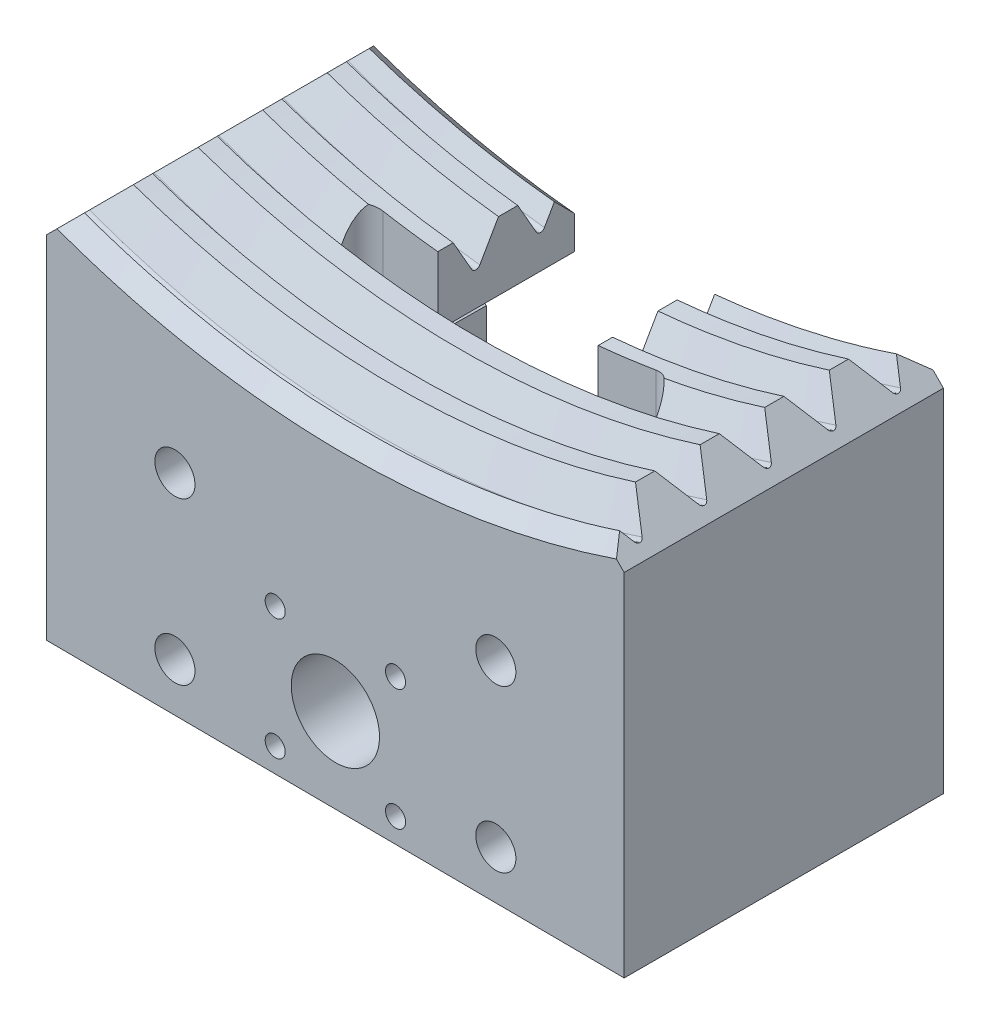
SolidWorks part; units mm, degrees
material "Nylon 101"
ref_plane "Ebene vorne" through (0, 0, 0) normal (0, 0, 1) x (1, 0, 0)
ref_plane "Ebene oben" through (0, 0, 0) normal (0, 1, 0) x (1, 0, 0)
ref_plane "Ebene rechts" through (0, 0, 0) normal (1, 0, 0) x (0, 0, -1)
sketch "Skizze1" plane through (0, 0, 0) normal (0, 0, 1) x (1, 0, 0)
  circle A0 centre (0, 0) radius 101
  circle A1 centre (0, 0) radius 225
  dimension "D1" = 202
  dimension "D2" = 450
extrude "Aufsatz-Linear austragen1" add sketch "Skizze1" along normal blind 40
chamfer "Fase1" distance 4.5 angle 45 2 edges at (101, 0, 40) (101, 0, 0)
sketch "Skizze32" plane through (0, 0, 40) normal (0, 0, 1) x (1, 0, 0)
  circle A0 centre (0, 0) radius 105
  dimension "D1" = 210
curve "Spirale/Helix1" pitch 8 height 50 turns 6.25
sketch "Skizze33" plane through (0, 0, 0) normal (1, 0, 0) x (0, 0, -1)
  line L0 (-40.5, 105.866) -> (-36.5, 98.9378) construction
  line L1 (-36.5, 98.9378) -> (-44.5, 98.9378) construction
  line L2 (-44.5, 98.9378) -> (-40.5, 105.866) construction
  line L3 (-40, 105) -> (-37.5, 100.6699)
  line L4 (-37.5, 100.6699) -> (-43.5, 100.6699)
  line L5 (-43.5, 100.6699) -> (-41, 105)
  line L6 (0, 0) -> (-68.055, 0) construction
  arc A0 (-40, 105) -> (-41, 105) centre (-40.5, 104.7113) ccw
  point P8 (0, 0)
sweep "Schnitt-Austragung1" cut profiles "Skizze33" path "Spirale/Helix1"
sketch "Skizze6" plane through (0, 0, 0) normal (0, 0, -1) x (-1, 0, 0)
  line L0 (0, 0) -> (0, -225) construction
  line L1 (-36, -143.9622) -> (36, -143.9622)
  line L2 (36, -143.9622) -> (36, -100.4622)
  line L3 (36, -100.4622) -> (31.5, -95.9622)
  line L4 (-36, -143.9622) -> (-36, -100.4622)
  line L5 (-36, -100.4622) -> (-34.6543, -99.1165)
  line L6 (31.5, -95.9622) -> (0, -64.4622)
  line L7 (0, -64.4622) -> (-34.6543, -99.1165)
  line L8 (0, -143.9622) -> (0, -102.9094) construction
  circle A0 centre (0, 0) radius 225 construction
  dimension "D1" = 45
  dimension "D2" = 45
  dimension "D3" = 48
  dimension "D4" = 43.5
  dimension "D5" = 72
  dimension "D6" = 34.6543
  dimension "D7" = 45.5817
extrude "Schnitt-Linear austragen1" cut sketch "Skizze6" against normal blind 40 flip side to cut
hole_wizard "Ø5.0 (5) Durchmesser Bohrung1" positions "Skizze8" profile "Skizze9" hole size "Ø5.0" standard "DIN" end condition through all
sketch "Skizze8" plane through (0, 0, 40) normal (0, 0, 1) x (1, 0, 0)
  line L0 (36, -143.9622) -> (-36, -143.9622) construction
  line L1 (0, -109) -> (0, -143.9622) construction
  point P0 (20, -117.9622)
  point P2 (-20, -117.9622)
  point P4 (-20, -137.9622)
  point P6 (20, -137.9622)
  dimension "D1" = 40
  dimension "D2" = 20
  dimension "D3" = 6
sketch "Skizze9" plane through (20, -117.9622, 40) normal (1, 0, 0) x (0, -1, 0)
  line L0 (0, 0) -> (0, 40)
  line L1 (0, 40) -> (2.5, 40)
  line L2 (2.5, 40) -> (2.5, 0)
  line L5 (2.5, 0) -> (0, 0)
  line L11 (0, -6.35) -> (0, 107.95) construction
  dimension "Bohrerdurchmesser" = 5
  dimension "Bohrungstiefe" = 40
hole_wizard "M3 Gewindebohrung1" positions "Skizze10" profile "Skizze11" tap size "M3" standard "DIN"
sketch "Skizze10" plane through (0, 0, 40) normal (0, 0, 1) x (1, 0, 0)
  line L0 (0, -143.9622) -> (0, -109) construction
  line L1 (36, -143.9622) -> (-36, -143.9622) construction
  point P0 (-7.5, -125.9622)
  point P2 (7.5, -125.9622)
  point P4 (7.5, -140.9622)
  point P6 (-7.5, -140.9622)
  dimension "D1" = 15
  dimension "D2" = 15
  dimension "D3" = 3
sketch "Skizze11" plane through (-7.5, -125.9622, 40) normal (1, 0, 0) x (0, -1, 0)
  line L0 (0, 0) -> (0, 11.2511)
  line L1 (0, 11.2511) -> (1.25, 10.5)
  line L2 (1.25, 10.5) -> (1.25, 0)
  line L5 (1.25, 0) -> (0, 0)
  line L10 (0, 11.2511) -> (-1.25, 10.5) construction
  line L11 (0, -6.35) -> (0, 107.95) construction
  dimension "Bohrerdurchmesser" = 2.5
  dimension "Bohrungstiefe" = 10.5
  dimension "Spitzenwinkel" = 118
cosmetic thread "Bohrungsgewinde110" parameters "D1"=6, "D2"=3
cosmetic thread "Bohrungsgewinde111" parameters "D1"=6, "D2"=3
cosmetic thread "Bohrungsgewinde112" parameters "D1"=6, "D2"=3
cosmetic thread "Bohrungsgewinde113" parameters "D1"=6, "D2"=3
hole_wizard "Ø11.0 (11) Durchmesser Bohrung1" positions "Skizze12" profile "Skizze13" hole size "Ø11.0" standard "DIN"
sketch "Skizze12" plane through (0, 0, 40) normal (0, 0, 1) x (1, 0, 0)
  line L0 (0, -143.9622) -> (0, -102.8349) construction
  line L1 (36, -143.9622) -> (-36, -143.9622) construction
  line L2 (-8.2479, -133.4622) -> (11.6618, -133.4622) construction
  point P0 (0, -133.4622)
sketch "Skizze13" plane through (0, -133.4622, 40) normal (1, 0, 0) x (0, -1, 0)
  line L0 (0, 0) -> (0, 28.8047)
  line L1 (0, 28.8047) -> (5.5, 25.5)
  line L2 (5.5, 25.5) -> (5.5, 0)
  line L5 (5.5, 0) -> (0, 0)
  line L10 (0, 28.8047) -> (-5.5, 25.5) construction
  line L11 (0, -6.35) -> (0, 107.95) construction
  dimension "Bohrerdurchmesser" = 11
  dimension "Bohrungstiefe" = 25.5
  dimension "Spitzenwinkel" = 118
hole_wizard "Ø12.0 (12) Durchmesser Bohrung1" positions "Skizze14" profile "Skizze15" hole size "Ø12.0" standard "DIN"
sketch "Skizze14" plane through (0, -143.9622, 0) normal (0, -1, 0) x (-1, 0, 0)
  line L0 (-36, -20) -> (36, -20) construction
  line L1 (-36, -40) -> (-36, 0) construction
  line L2 (36, -40) -> (36, 0) construction
  line L3 (0, 0) -> (0, -40) construction
  line L4 (-36, -40) -> (36, -40) construction
  point P0 (-22, -20)
  point P2 (22, -20)
  dimension "D1" = 44
sketch "Skizze15" plane through (22, -143.9622, 20) normal (1, 0, 0) x (0, 0, -1)
  line L0 (0, 0) -> (0, 37.1052)
  line L1 (0, 37.1052) -> (6, 33.5)
  line L2 (6, 33.5) -> (6, 0)
  line L5 (6, 0) -> (0, 0)
  line L10 (0, 37.1052) -> (-6, 33.5) construction
  line L11 (0, -6.35) -> (0, 107.95) construction
  dimension "Bohrerdurchmesser" = 12
  dimension "Bohrungstiefe" = 33.5
  dimension "Spitzenwinkel" = 118
sketch "Skizze16" plane through (0, -143.9622, 0) normal (0, -1, 0) x (1, 0, 0)
  line L0 (0, 40) -> (0, 0) construction
  line L1 (36, 40) -> (-36, 40) construction
  line L2 (-36, 20) -> (36, 20) construction
  line L3 (-36, 40) -> (-36, 0) construction
  line L4 (36, 40) -> (36, 0) construction
  circle A0 centre (0, 20) radius 5.5
  dimension "D1" = 11
extrude "Schnitt-Linear austragen2" cut sketch "Skizze16" against normal blind 3.2
hole_wizard "M4 Gewindebohrung1" positions "Skizze19" profile "Skizze18" tap size "M4" standard "DIN"
sketch "Skizze19" plane through (0, 0, 0) normal (0, 0, -1) x (-1, 0, 0)
  line L0 (0, -143.9622) -> (0, -108.1176) construction
  line L1 (-36, -143.9622) -> (36, -143.9622) construction
  point P0 (-6, -127.9622)
  point P2 (6, -127.9622)
  dimension "D1" = 12
  dimension "D2" = 16
sketch "Skizze18" plane through (6, -127.9622, 0) normal (1, 0, 0) x (0, 1, 0)
  line L0 (0, 0) -> (0, 30.9914)
  line L1 (0, 30.9914) -> (1.65, 30)
  line L2 (1.65, 30) -> (1.65, 0)
  line L5 (1.65, 0) -> (0, 0)
  line L10 (0, 30.9914) -> (-1.65, 30) construction
  line L11 (0, -6.35) -> (0, 107.95) construction
  dimension "Bohrerdurchmesser" = 3.3
  dimension "Bohrungstiefe" = 30
  dimension "Spitzenwinkel" = 118
cosmetic thread "Bohrungsgewinde114" parameters "D1"=8, "D2"=4
cosmetic thread "Bohrungsgewinde115" parameters "D1"=8, "D2"=4
sketch "Skizze20" plane through (0, 0, 0) normal (0, 0, -1) x (-1, 0, 0)
  line L0 (-36, -143.9622) -> (36, -143.9622) construction
  line L1 (-10, -143.9622) -> (10, -143.9622)
  line L2 (-10, -143.9622) -> (-10, -99.1502)
  line L3 (-10, -99.1502) -> (10, -99.1502)
  line L4 (10, -143.9622) -> (10, -99.1502)
  line L5 (-10, -143.9622) -> (10, -99.1502) construction
  line L6 (-10, -99.1502) -> (10, -143.9622) construction
  line L7 (0, -143.9622) -> (0, -102.8349) construction
  point P4 (0, -121.5562)
  dimension "D1" = 20
  dimension "D2" = 99.1502
extrude "Schnitt-Linear austragen3" cut sketch "Skizze20" against normal blind 19
sketch "Skizze21" plane through (0, 0, 19) normal (0, 0, -1) x (-1, 0, 0)
  line L0 (0, -103.2679) -> (0, -143.9622) construction
  line L1 (-5.5, -143.9622) -> (5.5, -143.9622) construction
  line L2 (5.4083, -143.9622) -> (10, -143.9622) construction
  line L3 (-6.5, -103.9622) -> (6.5, -103.9622)
  line L4 (-7.5, -104.9622) -> (-7.5, -120.9622)
  line L5 (-6.5, -121.9622) -> (6.5, -121.9622)
  line L6 (7.5, -104.9622) -> (7.5, -120.9622)
  line L7 (-7.5, -103.9622) -> (7.5, -121.9622) construction
  line L8 (-7.5, -121.9622) -> (7.5, -103.9622) construction
  arc A0 (-7.5, -120.9622) -> (-6.5, -121.9622) centre (-6.5, -120.9622) ccw
  arc A1 (-6.5, -103.9622) -> (-7.5, -104.9622) centre (-6.5, -104.9622) ccw
  arc A2 (6.5, -103.9622) -> (7.5, -104.9622) centre (6.5, -104.9622) cw
  arc A3 (6.5, -121.9622) -> (7.5, -120.9622) centre (6.5, -120.9622) ccw
  point P6 (0, -112.9622)
  dimension "D4" = 1
  dimension "D1" = 15
  dimension "D2" = 18
  dimension "D3" = 22
extrude "Schnitt-Linear austragen4" cut sketch "Skizze21" against normal blind 4.5
sketch "Skizze22" plane through (0, 0, 19) normal (0, 0, -1) x (-1, 0, 0)
  line L0 (0, -151.0346) -> (0, -103.2679) construction
  line L2 (-1.5, -124.7734) -> (1.5, -124.7734)
  line L3 (-1.5, -124.7734) -> (-1.5, -133.9803)
  line L4 (-1.5, -133.9803) -> (1.5, -133.9803)
  line L5 (1.5, -124.7734) -> (1.5, -133.9803)
  line L6 (-1.5, -124.7734) -> (1.5, -133.9803) construction
  line L7 (-1.5, -133.9803) -> (1.5, -124.7734) construction
  point P5 (0, -129.3769)
  dimension "D1" = 3
  dimension "D2" = 124.7734
  dimension "D3" = 129.3769
extrude "Schnitt-Linear austragen5" cut sketch "Skizze22" against normal blind 3.2
hole_wizard "Ø3.3 (3.3) Durchmesser Bohrung1" positions "Skizze25" profile "Skizze26" hole size "Ø3.3" standard "DIN"
sketch "Skizze25" plane through (0, 0, 0) normal (0, 1, 0) x (1, 0, 0)
  line L0 (0, 0) -> (0, -40) construction
  point P0 (-2.5, -20.2195)
  point P4 (2.5, -20.2805)
  dimension "D1" = 5
  dimension "D2" = 2.5
  dimension "D3" = 20.2195
  dimension "D4" = 20.2805
sketch "Skizze26" plane through (-2.5, 0, 20.2195) normal (1, 0, 0) x (0, 0, 1)
  line L0 (0, 0) -> (0, 128.5633)
  line L1 (0, 128.5633) -> (1.65, 128.5633)
  line L2 (1.65, 128.5633) -> (1.65, 0)
  line L5 (1.65, 0) -> (0, 0)
  line L11 (0, -6.35) -> (0, 107.95) construction
  dimension "Bohrerdurchmesser" = 3.3
  dimension "Bohrungstiefe" = 128.5633
sketch "Skizze28" plane through (0, 0, 0) normal (0, 1, 0) x (1, 0, 0)
  line L2 (-36, 0) -> (36, -0.453)
  line L4 (36, -0.453) -> (36, 0)
  line L5 (36, -40) -> (36, 0) construction
  line L6 (36, 0) -> (-36, 0)
extrude "Schnitt-Linear austragen7" cut sketch "Skizze28" against normal through all contours L2 L4 L6
sketch "Skizze29" plane through (0, 0, 0) normal (0, 1, 0) x (1, 0, 0)
  line L0 (36, -40) -> (-36, -39.547)
  line L2 (-36, -39.547) -> (-36, -40)
  line L3 (-36, -40) -> (-36, 0) construction
  line L4 (-36, -40) -> (36, -40)
  dimension "D1" = 39.547
extrude "Schnitt-Linear austragen8" cut sketch "Skizze29" against normal through all
sketch "Skizze30" plane through (-0.0014, 0, 0.2265) normal (0.0063, 0, -1) x (-1, 0, -0.0063)
  line L0 (35.9993, -143.9622) -> (9.9988, -143.9622) construction
  line L1 (-21.2358, -138.9622) -> (20.9642, -138.9622)
  line L2 (-21.2358, -138.9622) -> (-21.2358, -108.9622)
  line L3 (-21.2358, -108.9622) -> (20.9642, -108.9622)
  line L4 (20.9642, -138.9622) -> (20.9642, -108.9622)
  line L5 (-21.2358, -138.9622) -> (20.9642, -108.9622) construction
  line L6 (-21.2358, -108.9622) -> (20.9642, -138.9622) construction
  line L7 (-0.1258, -143.9622) -> (-0.1463, -102.8349) construction
  line L8 (-5.6258, -143.9622) -> (5.3742, -143.9622) construction
  point P4 (-0.1358, -123.9622)
  dimension "D1" = 30
  dimension "D2" = 5
  dimension "D3" = 42.2
  dimension "D4" = 20.9642
extrude "Schnitt-Linear austragen9" cut sketch "Skizze30" against normal blind 27
sketch "Skizze31" plane through (0, 0, 0) normal (0, 1, 0) x (1, 0, 0)
  line L0 (-16.8207, -19.5431) -> (17.1793, -19.7571) construction
  line L1 (-16.8049, -17.0432) -> (17.1951, -17.2571)
  line L2 (-16.8364, -22.0431) -> (17.1636, -22.257)
  line L4 (0, 0) -> (0.2961, -39.7754) construction
  arc A0 (-16.8049, -17.0432) -> (-16.8364, -22.0431) centre (-16.8207, -19.5431) ccw
  arc A1 (17.1636, -22.257) -> (17.1951, -17.2571) centre (17.1793, -19.7571) ccw
  point P2 (0.1793, -19.6501)
  dimension "D1" = 5
  dimension "D2" = 34
  dimension "D3" = 17
  dimension "D4" = 0.1793
  dimension "D5" = 17.1636
  dimension "D6" = 17.0432
extrude "Schnitt-Linear austragen10" cut sketch "Skizze31" against normal blind 126
equation "\"D3@Skizze33\"=\"D4@Skizze33\"/12"
equation "\"D5@Skizze33\"=\"D4@Skizze33\"/4"
